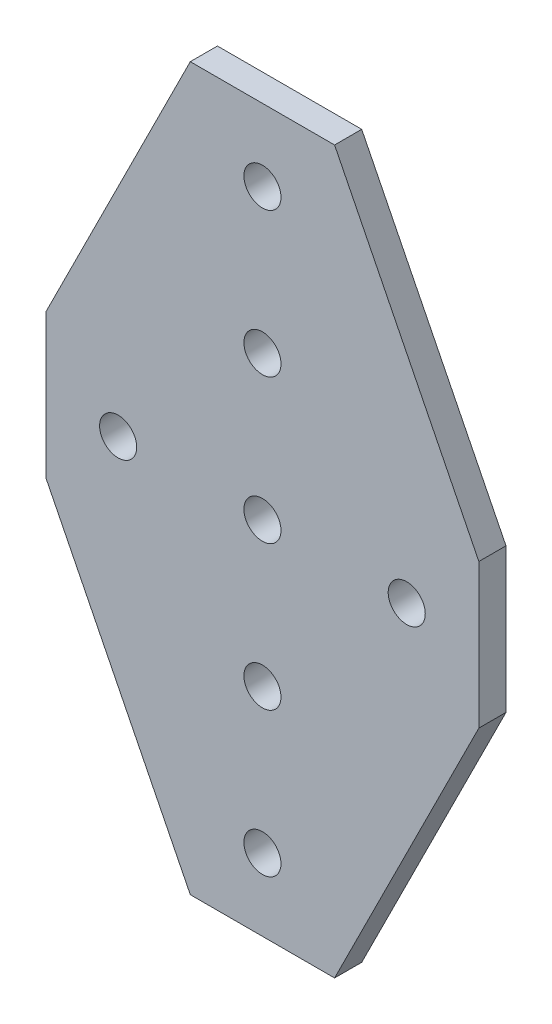
SolidWorks part; units mm, degrees
ref_plane "Front Plane" through (0, 0, 0) normal (0, 0, 1) x (1, 0, 0)
ref_plane "Top Plane" through (0, 0, 0) normal (0, 1, 0) x (1, 0, 0)
ref_plane "Right Plane" through (0, 0, 0) normal (1, 0, 0) x (0, 0, -1)
sketch "Sketch1" plane through (0, 0, 0) normal (0, 0, 1) x (1, 0, 0)
  line L0 (0, 63.5) -> (0, -63.5) construction
  line L1 (-38.1, 0) -> (38.1, 0) construction
  line L2 (12.7, 63.5) -> (-12.7, 63.5) construction
  line L3 (0, 54.0639) -> (0, 47.5361) construction
  line L4 (38.1, -12.7) -> (38.1, 12.7) construction
  point P0 (25.4, 0)
  point P3 (0, 25.4)
  point P4 (0, 0)
  point P8 (0, 0)
  point P11 (0, 63.5)
  point P14 (0, 50.8)
  point P17 (38.1, 0)
  point P19 (-25.4, -63.5)
  point P21 (-38.1, -63.5)
  dimension "D2" = 25.4
  dimension "D3" = 12.7
  dimension "D4" = 12.7
sketch "Sketch2" plane through (0, 0, 0) normal (1, 0, 0) x (0, 0, -1)
  line L0 (2.3876, 0) -> (-2.3876, 0) construction
  point P3 (0, 0)
  dimension "Thickness" = 4.7752
sketch "Sketch3" plane through (0, 0, 0) normal (0, 0, 1) x (1, 0, 0)
  line L0 (-12.7, 63.5) -> (12.7, 63.5)
  line L1 (12.7, 63.5) -> (38.1, 12.7)
  line L2 (38.1, 12.7) -> (38.1, -12.7)
  line L3 (38.1, -12.7) -> (12.7, -63.5)
  line L4 (12.7, -63.5) -> (-12.7, -63.5)
  line L5 (-12.7, -63.5) -> (-38.1, -12.7)
  line L6 (-38.1, -12.7) -> (-38.1, 12.7)
  line L7 (-38.1, 12.7) -> (-12.7, 63.5)
extrude "Boss-Extrude1" add sketch "Sketch3" against normal up to vertex (2.3876 mm away) and the other way up to vertex (2.3876 mm away) up to point (0, 0, -2.3876) other way up to point (0, 0, 2.3876)
sketch "Sketch4" plane through (0, 0, 2.3876) normal (0, 0, 1) x (1, 0, 0)
  line L0 (0, 50.8) -> (0, 25.4) construction
  line L1 (0, 63.5) -> (0, -63.5) construction
  line L2 (0, 63.5) -> (0, -63.5) construction
  circle A0 centre (0, 50.8) radius 3.2639
  circle A1 centre (0, 25.4) radius 3.2639
  circle A2 centre (0, 0) radius 3.2639
  circle A3 centre (0, -25.4) radius 3.2639
  circle A4 centre (0, -50.8) radius 3.2639
  dimension "D2" = 25.4
  dimension "D1" = 5
extrude "Cut-Extrude1" cut sketch "Sketch4" against normal through all both and the other way through all
pattern_linear "LPattern1" [suppressed] count 1 spacing 25.4
sketch "Sketch5" plane through (0, 0, 2.3876) normal (0, 0, 1) x (1, 0, 0)
  line L0 (0, 63.5) -> (0, -63.5) construction
  line L1 (0, 63.5) -> (0, -63.5) construction
  circle A0 centre (25.4, 0) radius 3.2639
  circle A1 centre (0, 0) radius 3.2639 construction
  circle A2 centre (-25.4, 0) radius 3.2639
extrude "Cut-Extrude2" cut sketch "Sketch5" against normal through all
pattern_linear "LPattern2" [suppressed] count 1 spacing 25.4
equation "\"D1@Sketch1\"=\"Hole to Edge@Sketch1\""
equation "\"D2@Sketch1\"=\"Flat@Sketch1\""
equation "\"D3@Sketch1\"=\"Hole to Edge@Sketch1\""
equation "\"D4@Sketch1\"=\"D3@Sketch1\""
equation "\"D2@Sketch4\"=\"Hole Spacing@Sketch1\""
equation "\"D1@Sketch4\"=\"#Vertical Holes@Sketch1\""
equation "\"D3@LPattern1\"=\"Hole Spacing@Sketch1\""
equation "\"D1@LPattern1\"=\"#Stacked Holes@Sketch1\""
equation "\"D3@LPattern2\"=\"Hole Spacing@Sketch1\""
equation "\"D1@LPattern2\"=\"#Stacked Holes@Sketch1\""
